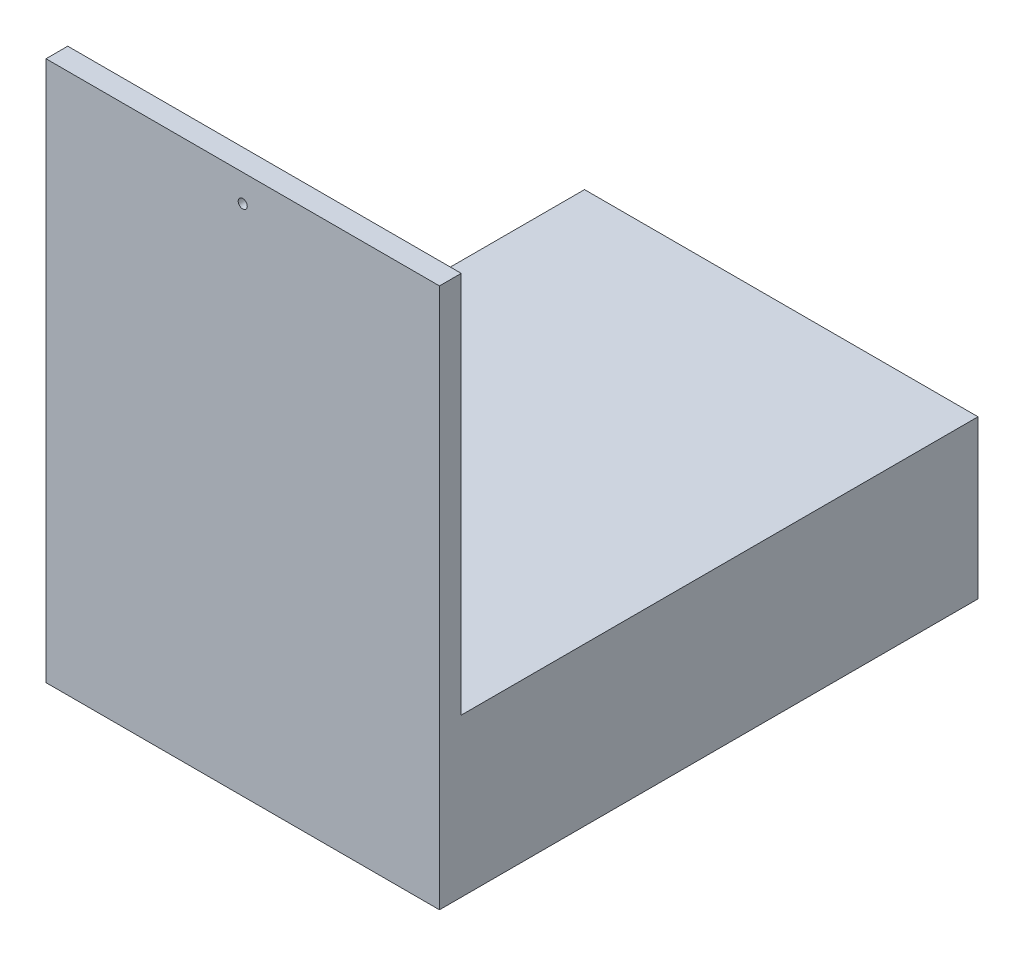
SolidWorks part; units mm, degrees
ref_plane "Front Plane" through (0, 0, 0) normal (0, 0, 1) x (1, 0, 0)
ref_plane "Top Plane" through (0, 0, 0) normal (0, 1, 0) x (1, 0, 0)
ref_plane "Right Plane" through (0, 0, 0) normal (1, 0, 0) x (0, 0, -1)
sketch "Sketch1" plane through (0, 0, 0) normal (0, 0, 1) x (1, 0, 0)
  line L0 (-108.5, 149) -> (108.5, 149)
  line L1 (-108.5, -149) -> (108.5, -149) construction
  line L2 (-108.5, -149) -> (-108.5, 149) construction
  line L3 (-108.5, 149) -> (108.5, 149) construction
  line L4 (108.5, -149) -> (108.5, 149) construction
  line L5 (-108.5, -149) -> (108.5, 149) construction
  line L6 (-108.5, 149) -> (108.5, -149) construction
  line L7 (-108.5, -149) -> (108.5, -149)
  line L8 (108.5, -149) -> (108.5, -107)
  line L9 (108.5, -107) -> (108.5, 149)
  line L10 (-108.5, -149) -> (-108.5, -107)
  line L11 (-108.5, -107) -> (-108.5, 149)
  point P0 (0, 0)
  point P9 (0, 149)
  dimension "D1" = 298
  dimension "D2" = 217
  dimension "D3" = 42
  dimension "D4" = 42
extrude "Boss-Extrude1" add sketch "Sketch1" along normal blind 12
sketch "Sketch2" plane through (0, 0, 0) normal (0, 0, -1) x (-1, 0, 0)
  line L0 (0, 149) -> (0, -149) construction
  line L1 (-108.5, 149) -> (108.5, 149) construction
  line L2 (108.5, -149) -> (-108.5, -149) construction
  circle A0 centre (0, 134) radius 2.5
  dimension "D1" = 5
  dimension "D2" = 15
extrude "Cut-Extrude1" cut sketch "Sketch2" against normal through all
sketch "Sketch3" plane through (0, 0, 0) normal (0, 0, -1) x (-1, 0, 0)
  line L1 (-108.5, -149) -> (108.5, -149)
  line L2 (-108.5, -149) -> (-108.5, -62)
  line L3 (-108.5, -62) -> (108.5, -62)
  line L4 (108.5, -149) -> (108.5, -62)
  line L5 (108.5, 149) -> (108.5, -149) construction
  dimension "D1" = 87
  dimension "D2" = 217
extrude "Boss-Extrude2" add sketch "Sketch3" along normal blind 285
